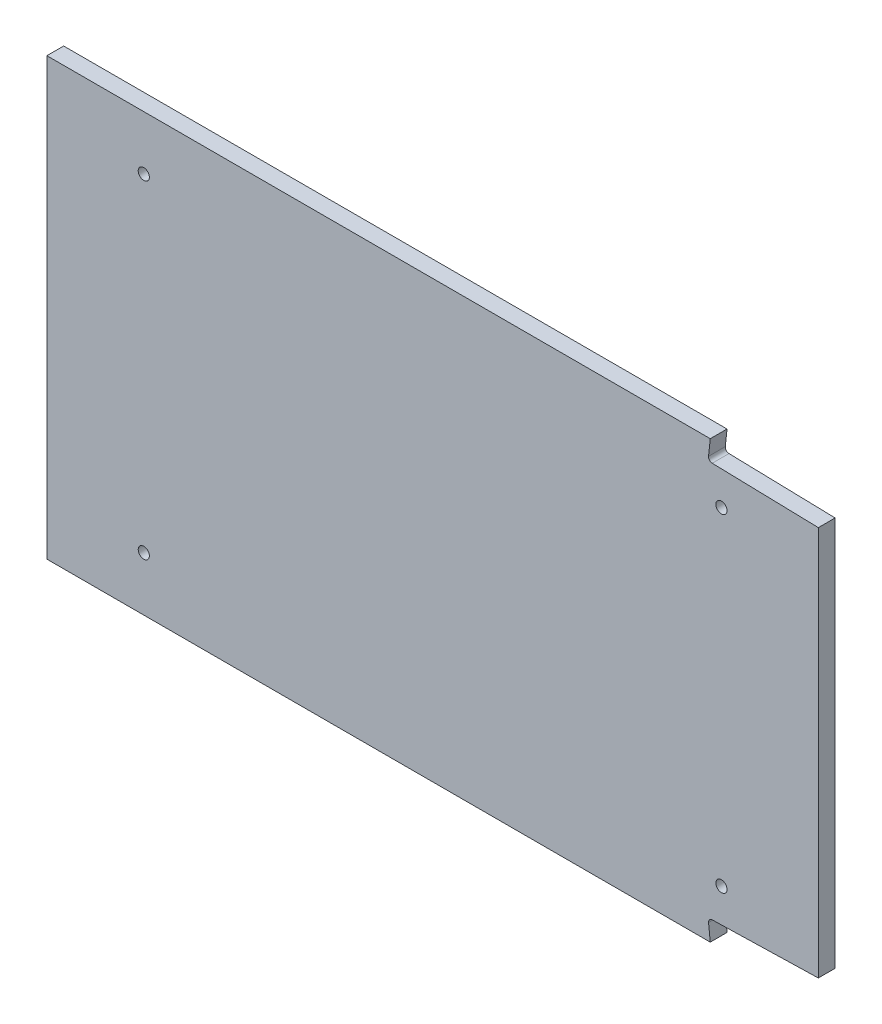
SolidWorks part; units mm, degrees
material "ABS"
ref_plane "Front Plane" through (0, 0, 0) normal (0, 0, 1) x (1, 0, 0)
ref_plane "Top Plane" through (0, 0, 0) normal (0, 1, 0) x (1, 0, 0)
ref_plane "Right Plane" through (0, 0, 0) normal (1, 0, 0) x (0, 0, -1)
sketch "Sketch1" plane through (0, 0, 0) normal (0, 0, 1) x (1, 0, 0)
  line L1 (103.5, -58.5) -> (-103.5, -58.5)
  line L2 (103.5, -58.5) -> (103.5, 58.5)
  line L3 (103.5, 58.5) -> (-103.5, 58.5)
  line L4 (-103.5, -58.5) -> (-103.5, 58.5)
  line L5 (103.5, -58.5) -> (-103.5, 58.5) construction
  line L6 (103.5, 58.5) -> (-103.5, -58.5) construction
  point P0 (0, 0)
  dimension "D1" = 207
  dimension "D2" = 117
extrude "Boss-Extrude1" add sketch "Sketch1" along normal blind 4.5
sketch "Sketch2" plane through (0, 0, 4.5) normal (0, 0, 1) x (1, 0, 0)
  line L0 (103.5, 58.5) -> (-103.5, 58.5) construction
  line L1 (-103.5, 58.5) -> (-103.5, -58.5) construction
  circle A0 centre (-77.5, 44) radius 1.5
  dimension "D1" = 3
  dimension "D2" = 14.5
  dimension "D3" = 26
extrude "Cut-Extrude1" cut sketch "Sketch2" against normal through all
mirror "Mirror1" about plane through (0, 0, 0) normal (1, 0, 0) of "Cut-Extrude1"
mirror "Mirror3" about plane through (0, 0, 0) normal (0, 1, 0) of "Mirror1", "Cut-Extrude1"
sketch "Sketch3" plane through (0, 0, 4.5) normal (0, 0, 1) x (1, 0, 0)
  line L0 (74.5026, 58.5) -> (74.0418, 54.1784)
  line L1 (103.5, 58.5) -> (-103.5, 58.5) construction
  line L2 (75.0251, 53.0563) -> (103.5, 52.3309)
  line L3 (103.5, -58.5) -> (103.5, 58.5) construction
  line L4 (74.5026, 58.5) -> (103.5, 58.5)
  line L5 (103.5, 58.5) -> (103.5, 52.3309)
  arc A1 (74.0418, 54.1784) -> (75.0251, 53.0563) centre (75.0509, 54.0708) ccw
  circle A3 centre (-77.5, 44) radius 1.5 construction
  point P5 (74.5026, 58.5)
  point P7 (0, 0)
  point P11 (74.0418, 55.2483)
  point P12 (103.5, 53.4873)
  point P19 (103.5, 52.3309)
  dimension "D1" = 1.0148
  dimension "D2" = 151.5418
  dimension "D3" = 152.0026
  dimension "D4" = 152.5251
  dimension "D5" = 152.5509
extrude "Cut-Extrude2" cut sketch "Sketch3" against normal up to next (4.5 mm away)
mirror "Mirror4" about plane through (0, 0, 0) normal (0, 1, 0) of "Cut-Extrude2"
